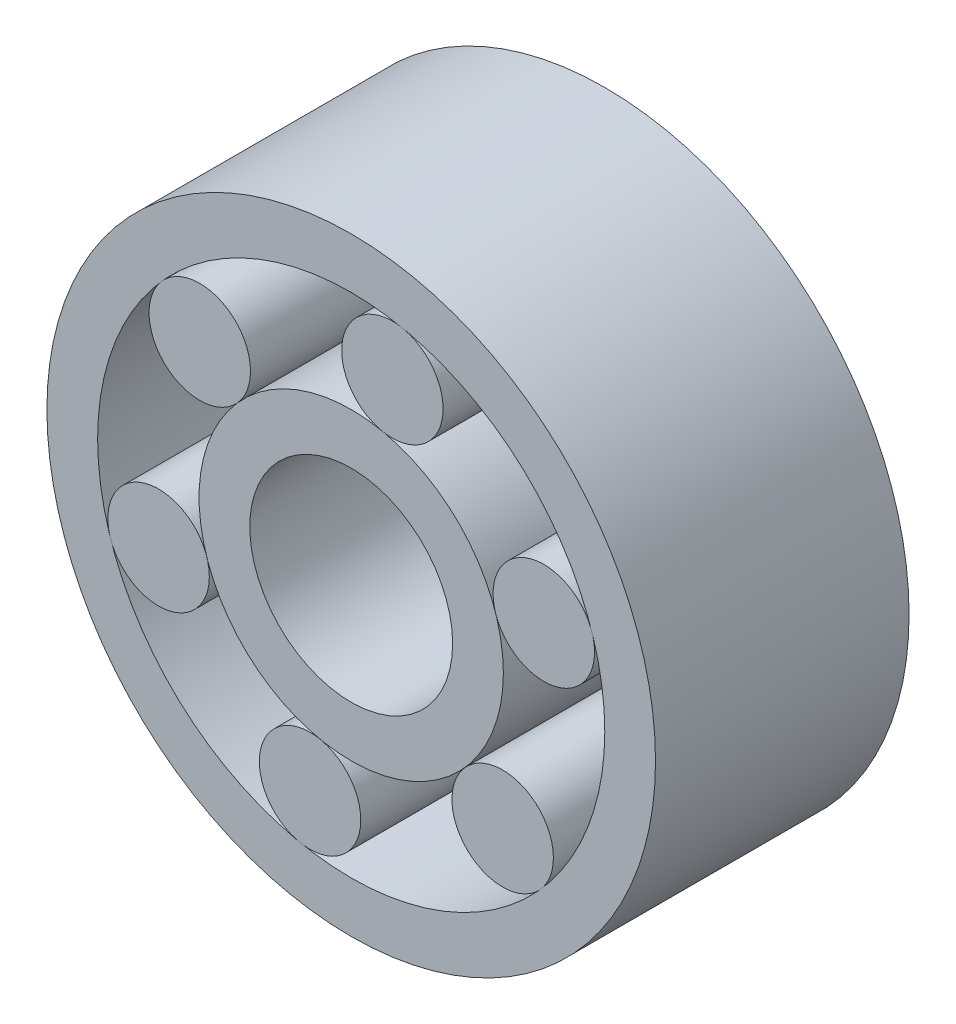
SolidWorks part; units mm, degrees
ref_plane "前视基准面" through (0, 0, 0) normal (0, 0, 1) x (1, 0, 0)
ref_plane "上视基准面" through (0, 0, 0) normal (0, 1, 0) x (1, 0, 0)
ref_plane "右视基准面" through (0, 0, 0) normal (1, 0, 0) x (0, 0, -1)
sketch "草图1" plane through (0, 0, 0) normal (0, 0, 1) x (1, 0, 0)
  circle A0 centre (0, 0) radius 3
  circle A1 centre (0, 0) radius 1
  circle A2 centre (0, 0) radius 2.5
  circle A3 centre (0, 0) radius 1.5
  dimension "D1" = 6
  dimension "D2" = 2
  dimension "D3" = 5
  dimension "D4" = 3
extrude "凸台-拉伸1" add sketch "草图1" along normal blind 2.5 contours A0 A2 | A3 A1
sketch "草图2" plane through (0, 0, 0) normal (0, 0, 1) x (1, 0, 0)
  circle A0 centre (-1.4931, 1.3307) radius 0.5
  circle A1 centre (0, 0) radius 1.5 construction
  circle A2 centre (0, 0) radius 2.5 construction
  circle A3 centre (0.4058, 1.9584) radius 0.5
  circle A4 centre (1.8989, 0.6277) radius 0.5
  circle A5 centre (1.4931, -1.3307) radius 0.5
  circle A6 centre (-0.4058, -1.9584) radius 0.5
  circle A7 centre (-1.8989, -0.6277) radius 0.5
  point P18 (0, 0)
  dimension "D1" = 6
extrude "凸台-拉伸2" add sketch "草图2" along normal blind 2.5 separate body
